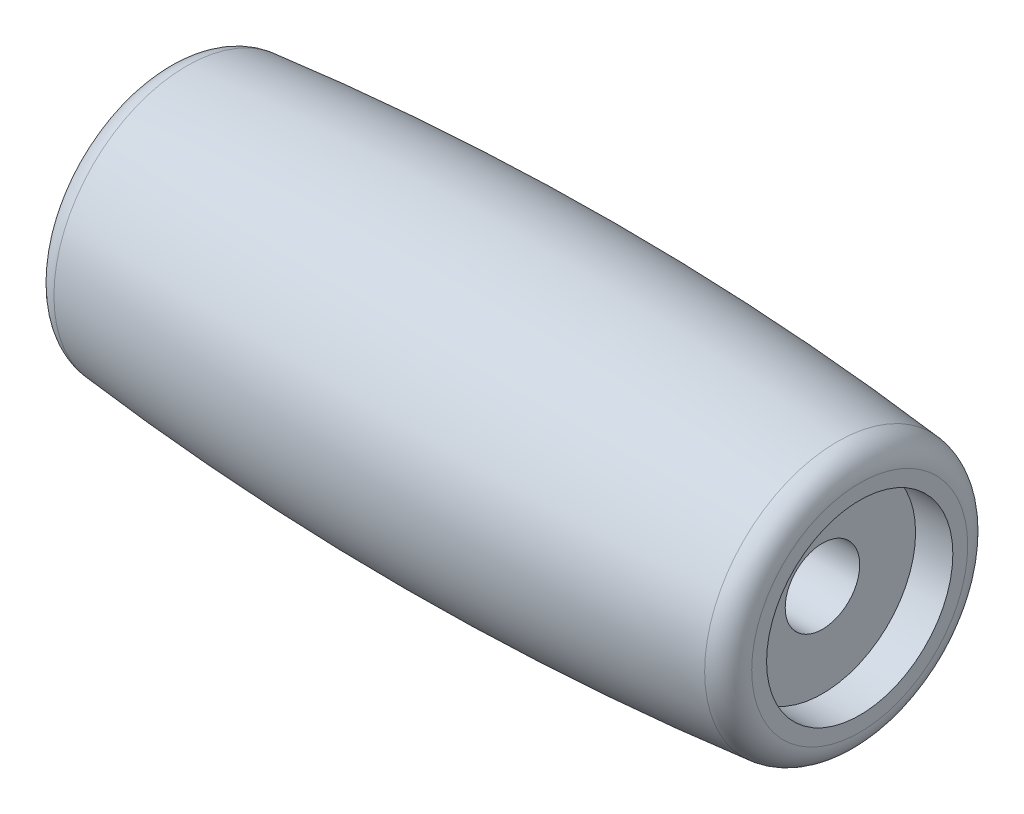
SolidWorks part; units mm, degrees
ref_plane "Front Plane" through (0, 0, 0) normal (0, 0, 1) x (1, 0, 0)
ref_plane "Top Plane" through (0, 0, 0) normal (0, 1, 0) x (1, 0, 0)
ref_plane "Right Plane" through (0, 0, 0) normal (1, 0, 0) x (0, 0, -1)
sketch "Sketch1" plane through (0, 0, 0) normal (0, 0, 1) x (1, 0, 0)
  line L0 (-14, 0) -> (14, 0) construction
  line L1 (14, 4.3486) -> (14, 3.75)
  line L2 (0, 0) -> (0, 6) construction
  line L3 (-14, 4.3486) -> (-14, 3.75)
  line L4 (12.5, 1.5) -> (-9.0908, 1.5)
  line L5 (14, 3.75) -> (12.5, 3.75)
  line L8 (12.5, 3.75) -> (12.5, 1.5)
  line L9 (-14, 3.75) -> (-12.5, 3.75)
  line L10 (-12.5, 3.75) -> (-12.5, 1.5)
  line L11 (-12.5, 1.5) -> (9.0908, 1.5)
  arc A0 (-13.1, 5.3436) -> (13.1, 5.3436) centre (0, -125.0417) cw
  arc A3 (-14, 4.3486) -> (-13.1, 5.3436) centre (-13, 4.3486) cw
  arc A5 (14, 4.3486) -> (13.1, 5.3436) centre (13, 4.3486) ccw
  arc A6 (-14, 4.3486) -> (-13.1, 5.3436) centre (-13, 4.3486) cw
  point P0 (-14, 0)
  point P6 (14, 0)
  point P9 (-14, 1.5)
  point P21 (-14, -5.25)
  point P24 (-14, 5.25)
  point P27 (14, -5.25)
  point P30 (14, 5.25)
  dimension "D1" = 3.75
  dimension "D3" = 14
  dimension "D4" = 6
  dimension "D5" = 1.5
  dimension "D7" = 1.5
  dimension "D8" = 1.5
revolve "Revolve1" add sketch "Sketch1" angle 360 about L0
scale "Scale1" bodies to scale 101 scale about centroid uniform scaling yes scale factor 2
